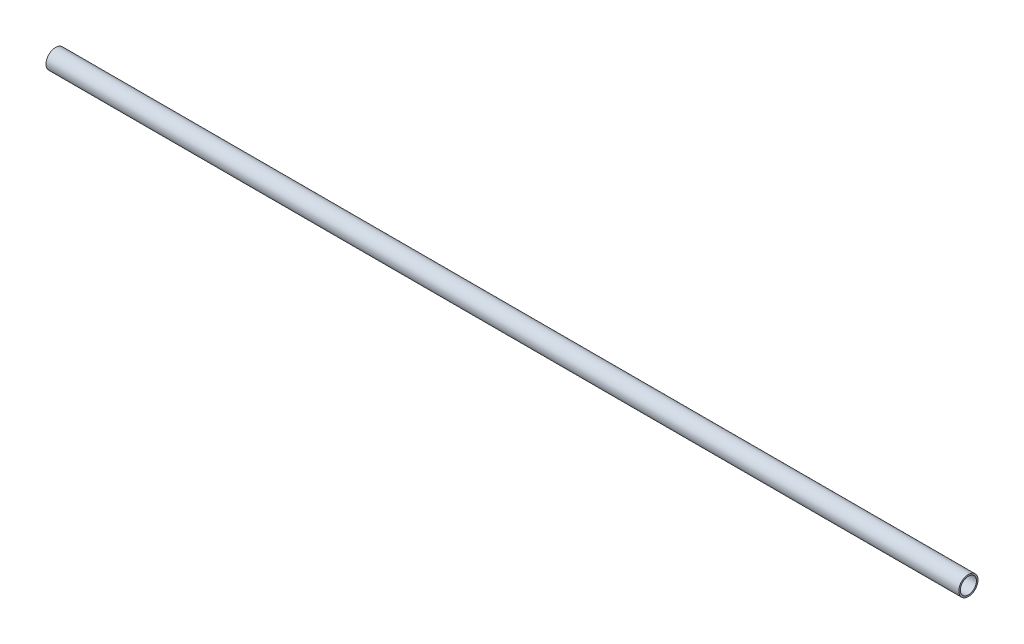
SolidWorks part; units mm, degrees
ref_plane "Front Plane" through (0, 0, 0) normal (0, 0, 1) x (1, 0, 0)
ref_plane "Top Plane" through (0, 0, 0) normal (0, 1, 0) x (1, 0, 0)
ref_plane "Right Plane" through (0, 0, 0) normal (1, 0, 0) x (0, 0, -1)
sketch "Sketch1" plane through (0, 0, 0) normal (1, 0, 0) x (0, 0, -1)
  circle A0 centre (0, 0) radius 3.175
  circle A1 centre (0, 0) radius 2.667
  dimension "D1" = 6.35
  dimension "D2" = 0.508
extrude "Boss-Extrude1" add sketch "Sketch1" against normal blind 301.625
move or copy body "Body-Move/Copy1" [suppressed] bodies to move or copy 101 parameters "D1"=0, "D2"=0, "D3"=0
